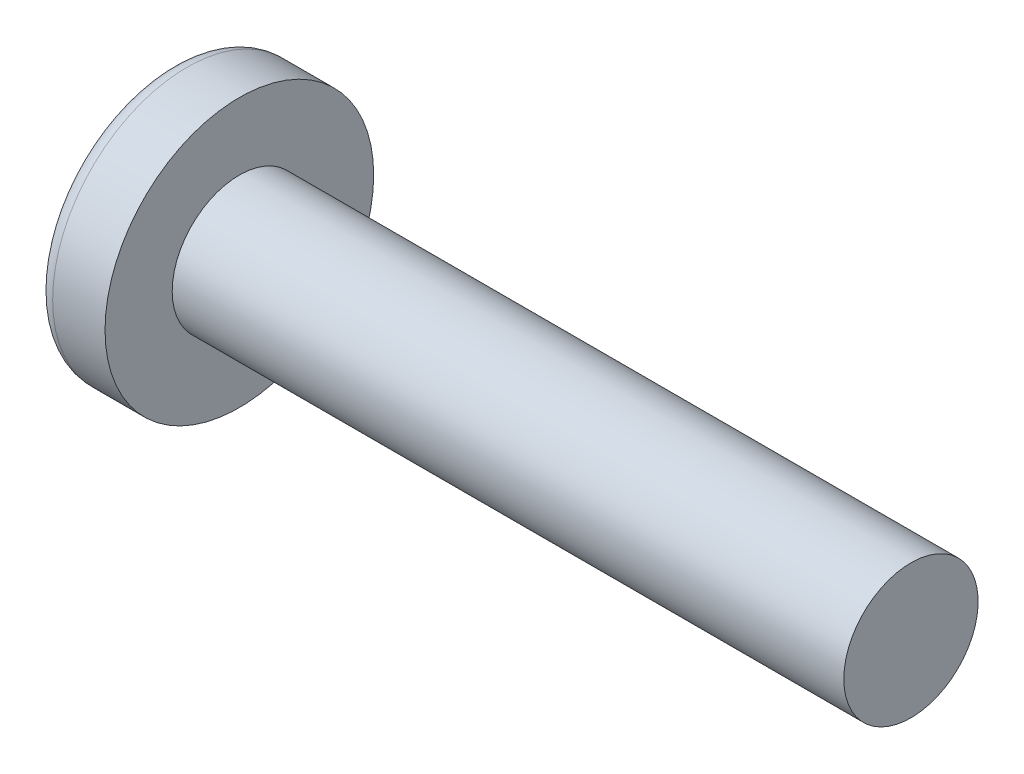
SolidWorks part; units mm, degrees
material "Plain Carbon Steel"
ref_plane "Plane1" through (0, 0, 0) normal (0, 0, 1) x (1, 0, 0)
ref_plane "Plane2" through (0, 0, 0) normal (0, 1, 0) x (1, 0, 0)
ref_plane "Plane3" through (0, 0, 0) normal (1, 0, 0) x (0, 0, -1)
sketch "BodySke" plane through (0, 0, 0) normal (0, 0, 1) x (1, 0, 0)
  line L0 (1.6, 1) -> (1.6, 2)
  line L1 (2, 6.35) -> (2, -3.175) construction
  line L2 (-25.4, 0) -> (127, 0) construction
  line L3 (11.6, 0) -> (0, 0)
  line L4 (1.6, 1) -> (11.6, 1)
  line L5 (11.6, 1) -> (11.6, 0)
  line L6 (0.8201, 2) -> (1.6, 2)
  line L7 (1.6, -1) -> (11.6, -1) construction
  line L8 (1.6, 6.35) -> (1.6, -3.175) construction
  arc A0 (0.6271, 1.9027) -> (0, 0) centre (3.2, 0) ccw
  arc A2 (0.6271, 1.9027) -> (0.8201, 2) centre (0.8201, 1.76) cw
  dimension "Head_crown_rad" = 3.2
  dimension "Head_fillet_rad" = 0.24
  dimension "Diameter" = 2
  dimension "Length" = 10
  dimension "Head_ht" = 1.6
  dimension "Head_dia" = 4
  dimension "Advance" = 0.4
  dimension "Thread_nom" = 10
revolve "Base-Revolve" add sketch "BodySke" angle 360 about L2
cosmetic thread "ThreadCosmetic" [suppressed] parameters "Thread_length"=9.6, "Thread_minor"=1.548
sketch "Sketch3" plane through (0, 0, 0) normal (1, 0, 0) x (0, 0, -1)
  line L0 (0.24, -0.91) -> (-0.24, -0.91)
  line L1 (0.24, -0.91) -> (0.24, 0.91)
  line L2 (-0.24, 0.91) -> (0.24, 0.91)
  line L3 (-0.24, 0.91) -> (-0.24, -0.91)
  dimension "Cross_dia" = 1.82
  dimension "D1" = 0.91
  dimension "Cross_width" = 0.48
  dimension "D2" = 0.24
ref_plane "Plane4" through (1.19, 0, 0) normal (1, 0, 0) x (0, 0, -1)
sketch "Sketch4" plane through (1.19, 0, 0) normal (1, 0, 0) x (0, 0, -1)
  line L0 (0.12, -0.12) -> (-0.12, -0.12)
  line L1 (0.12, -0.12) -> (0.12, 0.12)
  line L2 (-0.12, 0.12) -> (0.12, 0.12)
  line L3 (-0.12, 0.12) -> (-0.12, -0.12)
  dimension "D2" = 0.24
  dimension "D1" = 0.24
  dimension "D3" = 0.12
  dimension "D4" = 0.12
loft "Cut-Loft1" cut profiles "Sketch3", "Sketch4"
pattern_circular "CirPattern1" count 2 every 90 about axis through (0, 0, 0) along (1, 0, 0) of "Cut-Loft1"
sketch "ThdSchSke" plane through (0, 0, 0) normal (0, 0, 1) x (1, 0, 0)
  line L0 (2, -0.774) -> (1.8418, -1)
  line L1 (2, -0.774) -> (2.1582, -1)
  line L2 (2.1582, -1) -> (2.1582, -1.25)
  line L3 (-3.175, 0) -> (5.1513, 0) construction
  line L5 (2.1582, -1.25) -> (1.8418, -1.25)
  line L6 (1.8418, -1.25) -> (1.8418, -1)
  dimension "Diameter" = 2
  dimension "SideAngle" = 55
  dimension "VeeAngle" = 70
  dimension "Thread_minor" = 1.548
  dimension "Overcut" = 2.5
  dimension "Start" = 2
revolve "ThreadSchematic" [suppressed] cut sketch "ThdSchSke" angle 360 about L3
pattern_linear "ThdSchPat" [suppressed]
equation "\"D1@Sketch3\" = \"Cross_dia@Sketch3\" / 2"
equation "\"D2@Sketch3\" = \"Cross_width@Sketch3\" / 2"
equation "\"D1@Sketch4\" = \"Cross_width@Sketch3\" *.5"
equation "\"D2@Sketch4\" = \"D1@Sketch4\""
equation "\"D3@Sketch4\" = \"D1@Sketch4\" / 2"
equation "\"D4@Sketch4\" = \"D2@Sketch4\" / 2"
equation "\"Thread_length@ThreadCosmetic\" = ((sgn( (\"Length@BodySke\" - \"Advance@BodySke\" ) - \"Thread_nom@BodySke\" )-1)*( (\"Length@BodySke\" - \"Advance@BodySke\" ) - \"Thread_nom@BodySke\" ))/-2+ \"Thread_nom@BodySke\""
equation "\"Thread_minor@ThdSchSke\" = \"Thread_minor@ThreadCosmetic\""
equation "\"Diameter@ThdSchSke\" = \"Diameter@BodySke\""
equation "\"Overcut@ThdSchSke\" = \"Diameter@BodySke\" * 1.25"
equation "\"Start@ThdSchSke\" = \"Head_ht@BodySke\" + \"Length@BodySke\" - \"Thread_length@ThreadCosmetic\"  '---Non-countersunk---"
equation "\"Num_threads@ThdSchPat\" = int( \"Thread_length@ThreadCosmetic\" / \"Advance@BodySke\" + 0.999 )  + 1"
equation "\"Advance@ThdSchPat\" = \"Thread_length@ThreadCosmetic\" /  (\"Num_threads@ThdSchPat\" - 1) 'relax it"
